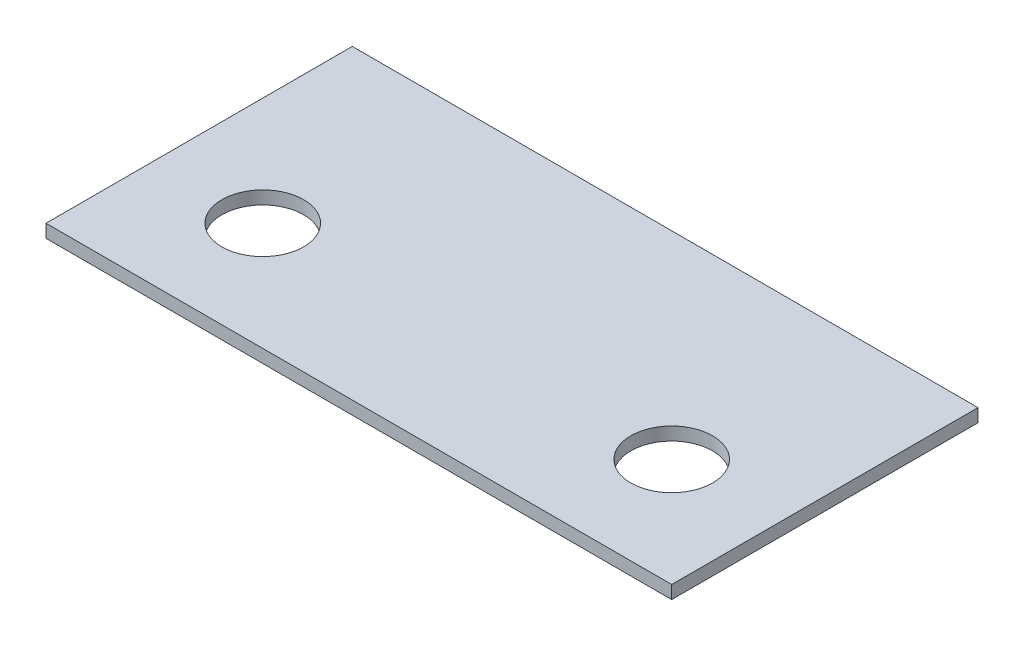
SolidWorks part; units mm, degrees
ref_plane "Front Plane" through (0, 0, 0) normal (0, 0, 1) x (1, 0, 0)
ref_plane "Top Plane" through (0, 0, 0) normal (0, 1, 0) x (1, 0, 0)
ref_plane "Right Plane" through (0, 0, 0) normal (1, 0, 0) x (0, 0, -1)
sketch "Sketch1" plane through (0, 0, 0) normal (0, 1, 0) x (1, 0, 0)
  line L1 (-382.5, 187.25) -> (382.5, 187.25)
  line L2 (-382.5, 187.25) -> (-382.5, -187.25)
  line L3 (-382.5, -187.25) -> (382.5, -187.25)
  line L4 (382.5, 187.25) -> (382.5, -187.25)
  line L5 (-382.5, 187.25) -> (382.5, -187.25) construction
  line L6 (-382.5, -187.25) -> (382.5, 187.25) construction
  point P0 (0, 0)
  dimension "D1" = 374.5
  dimension "D2" = 765
extrude "Boss-Extrude1" add sketch "Sketch1" along normal blind 16
sketch "Sketch2" plane through (0, 16, 0) normal (0, 1, 0) x (1, 0, 0)
  line L0 (-382.5, -54.75) -> (382.5, -54.75) construction
  line L2 (382.5, -187.25) -> (382.5, 187.25) construction
  line L3 (0, -187.25) -> (0, 187.25) construction
  line L4 (-382.5, -187.25) -> (382.5, -187.25) construction
  line L5 (382.5, 187.25) -> (-382.5, 187.25) construction
  line L6 (-382.5, 195.25) -> (382.5, 195.25) construction
  line L7 (-382.5, -187.25) -> (382.5, -187.25)
  line L8 (-382.5, -187.25) -> (-382.5, 577.75)
  line L9 (-382.5, 577.75) -> (382.5, 577.75)
  line L10 (382.5, -187.25) -> (382.5, 577.75)
  circle A0 centre (-250, -54.75) radius 50
  circle A1 centre (250, -54.75) radius 50
  dimension "D1" = 100
  dimension "D2" = 500
  dimension "D3" = 500
extrude "Cut-Extrude1" cut sketch "Sketch2" against normal up to next and the other way through all contours A0 | A1
